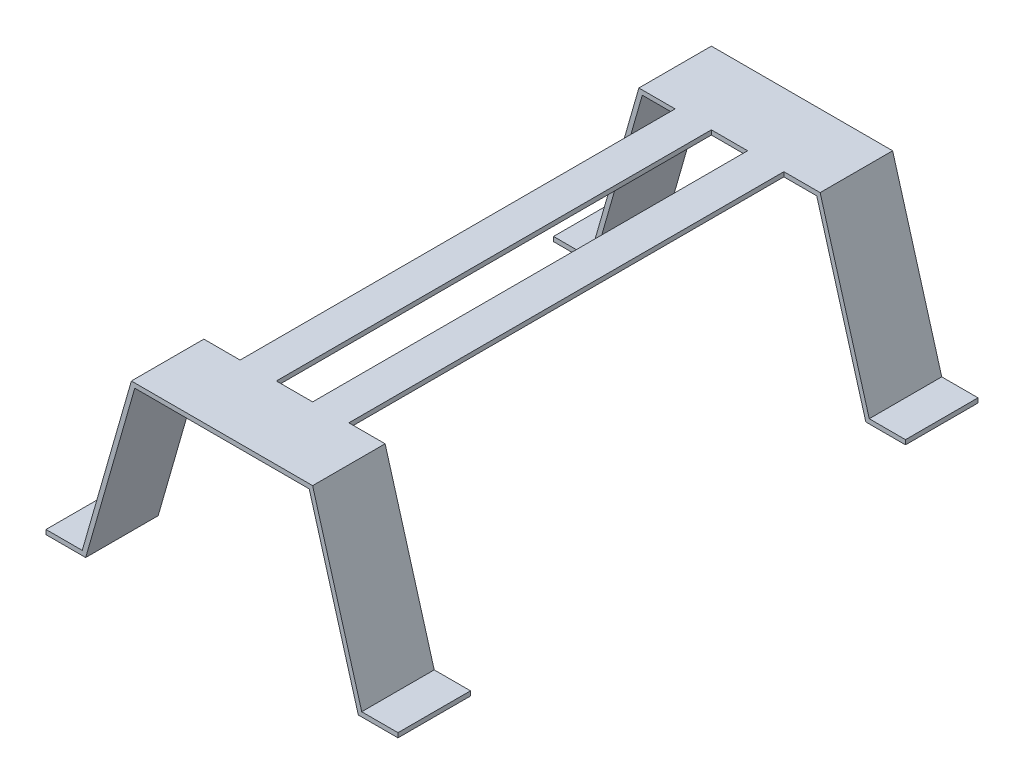
SolidWorks part; units mm, degrees
ref_plane "Front" through (0, 0, 0) normal (0, 0, 1) x (1, 0, 0)
ref_plane "Top" through (0, 0, 0) normal (0, 1, 0) x (1, 0, 0)
ref_plane "Right" through (0, 0, 0) normal (1, 0, 0) x (0, 0, -1)
sketch "Sketch1" plane through (0, 0, 0) normal (0, 0, 1) x (1, 0, 0)
  line L0 (-29.7868, -3.8372) -> (-4.3868, -3.8372)
  line L5 (-4.3868, -3.8372) -> (30.0226, 116.1628)
  line L6 (30.0226, 116.1628) -> (157.0226, 116.1628)
  line L7 (-29.7868, -7.0122) -> (-1.9943, -7.0122)
  line L8 (157.0226, 116.1628) -> (191.4321, -3.8372)
  line L9 (191.4321, -3.8372) -> (216.8321, -3.8372)
  line L10 (-1.9943, -7.0122) -> (32.4151, 112.9878)
  line L11 (32.4151, 112.9878) -> (154.6301, 112.9878)
  line L12 (154.6301, 112.9878) -> (189.0395, -7.0122)
  line L13 (189.0395, -7.0122) -> (216.8321, -7.0122)
  line L14 (-29.7868, -3.8372) -> (-29.7868, -7.0122)
  line L15 (216.8321, -3.8372) -> (216.8321, -7.0122)
  dimension "D1" = 106
  dimension "D2" = 127
  dimension "D3" = 120
  dimension "D4" = 106
  dimension "D5" = 120
  dimension "D6" = 25.4
  dimension "D7" = 25.4
  dimension "D8" = 3.175
extrude "Boss-Extrude1" add sketch "Sketch1" along normal blind 50.8
sketch "Sketch2" plane through (0, 0, 50.8) normal (0, 0, 1) x (1, 0, 0)
  line L0 (157.0226, 116.1628) -> (30.0226, 116.1628) construction
  line L1 (55.4226, 116.1628) -> (80.8226, 116.1628)
  line L2 (55.4226, 116.1628) -> (55.4226, 112.9878)
  line L3 (55.4226, 112.9878) -> (80.8226, 112.9878)
  line L4 (80.8226, 116.1628) -> (80.8226, 112.9878)
  line L5 (32.4151, 112.9878) -> (154.6301, 112.9878) construction
  line L7 (106.2226, 116.1628) -> (131.6226, 116.1628)
  line L8 (106.2226, 116.1628) -> (106.2226, 112.9878)
  line L9 (106.2226, 112.9878) -> (131.6226, 112.9878)
  line L10 (131.6226, 116.1628) -> (131.6226, 112.9878)
  dimension "D1" = 25.4
  dimension "D2" = 25.4
  dimension "D3" = 25.4
  dimension "D4" = 25.4
extrude "Boss-Extrude2" add sketch "Sketch2" along normal blind 304.8
sketch "Sketch4" plane through (0, 0, 355.6) normal (0, 0, 1) x (1, 0, 0)
  line L0 (30.0226, 116.1628) -> (157.0226, 116.1628)
  line L1 (191.4321, -3.8372) -> (157.0226, 116.1628) construction
  line L2 (157.0226, 116.1628) -> (191.4321, -3.8372)
  line L3 (191.4321, -3.8372) -> (216.8321, -3.8372)
  line L4 (216.8321, -3.8372) -> (216.8321, -7.0122)
  line L5 (216.8321, -7.0122) -> (189.0395, -7.0122)
  line L6 (189.0395, -7.0122) -> (154.6301, 112.9878)
  line L7 (154.6301, 112.9878) -> (32.4151, 112.9878)
  line L8 (32.4151, 112.9878) -> (-1.9943, -7.0122)
  line L9 (-1.9943, -7.0122) -> (-29.7868, -7.0122)
  line L10 (-29.7868, -7.0122) -> (-29.7868, -3.8372)
  line L11 (-29.7868, -3.8372) -> (-4.3868, -3.8372)
  line L12 (-4.3868, -3.8372) -> (30.0226, 116.1628)
extrude "Boss-Extrude4" add sketch "Sketch4" along normal blind 50.8
